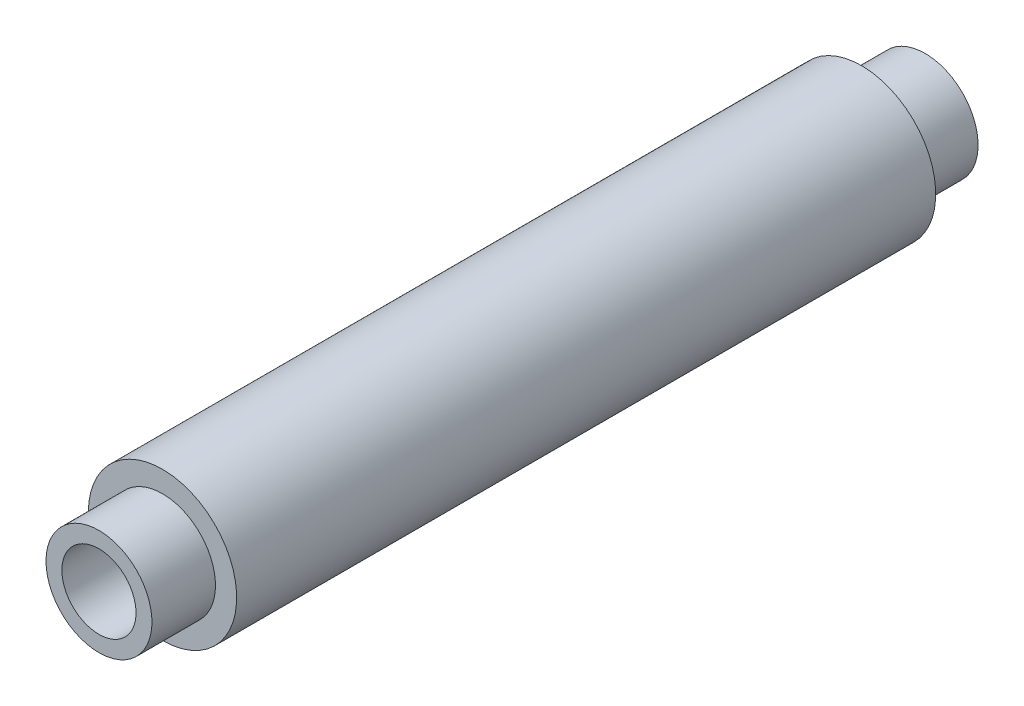
SolidWorks part; units mm, degrees
ref_plane "Front Plane" through (0, 0, 0) normal (0, 0, 1) x (1, 0, 0)
ref_plane "Top Plane" through (0, 0, 0) normal (0, 1, 0) x (1, 0, 0)
ref_plane "Right Plane" through (0, 0, 0) normal (1, 0, 0) x (0, 0, -1)
sketch "Sketch1" plane through (0, 0, 0) normal (0, 1, 0) x (1, 0, 0)
  line L0 (0, 21.3766) -> (0, -23.63) construction
  line L1 (0, 16.5) -> (2.5, 16.5) construction
  line L2 (3.5, 16.5) -> (3.5, -16.5)
  line L3 (3.5, -16.5) -> (2.5, -16.5)
  line L4 (0, -16.5) -> (0, 16.5)
  line L5 (2.5, 16.5) -> (2.5, 19.5)
  line L6 (2.5, 19.5) -> (0, 19.5)
  line L7 (0, 19.5) -> (0, 16.5)
  line L8 (2.5, 16.5) -> (3.5, 16.5)
  line L9 (-10.4172, 0) -> (20.3875, 0) construction
  line L11 (0, -19.5) -> (0, -16.5)
  line L12 (2.5, -19.5) -> (0, -19.5)
  line L13 (2.5, -16.5) -> (2.5, -19.5)
  line L14 (2.5, -16.5) -> (0, -16.5) construction
  dimension "D1" = 7
  dimension "D2" = 33
  dimension "D3" = 5
  dimension "D4" = 3
revolve "Revolve1" add sketch "Sketch1" angle 360 about L0
shell "Shell1" thickness 0.75
